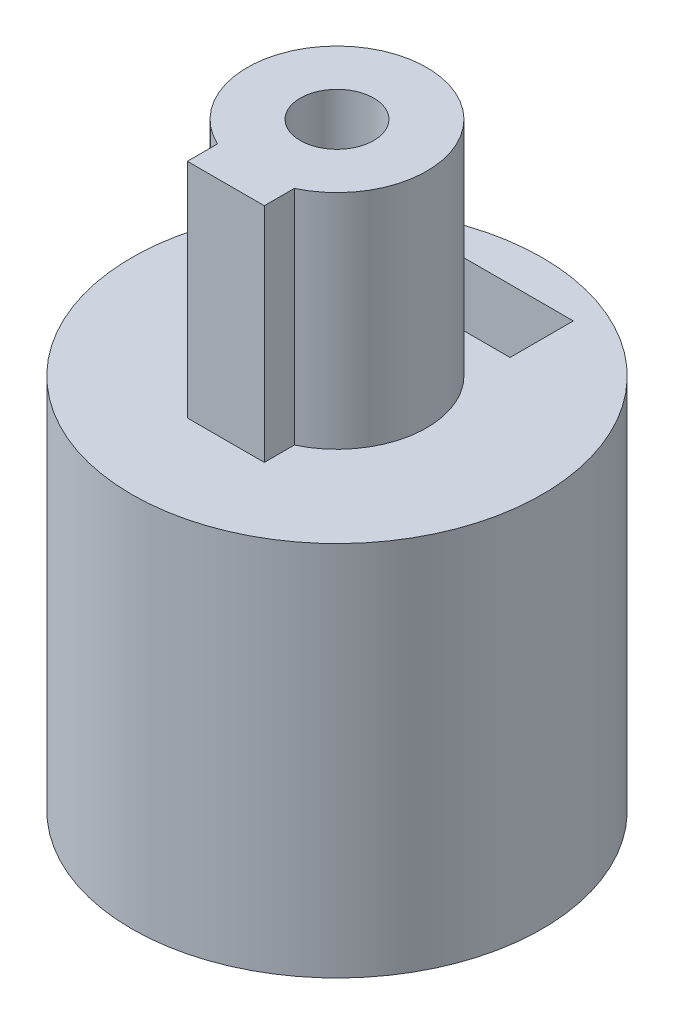
SolidWorks part; units mm, degrees
ref_plane "Front Plane" through (0, 0, 0) normal (0, 0, 1) x (1, 0, 0)
ref_plane "Top Plane" through (0, 0, 0) normal (0, 1, 0) x (1, 0, 0)
ref_plane "Right Plane" through (0, 0, 0) normal (1, 0, 0) x (0, 0, -1)
sketch "Sketch1" plane through (0, 0, 0) normal (0, 1, 0) x (1, 0, 0)
  circle A0 centre (0, 0) radius 1.965 construction
  circle A1 centre (0, 0) radius 6
  dimension "D1" = 3.93
  dimension "D2" = 12
extrude "Boss-Extrude1" add sketch "Sketch1" along normal blind 10
sketch "Sketch2" plane through (0, 0, 0) normal (0, 0, 1) x (1, 0, 0)
  line L0 (0, 10) -> (0, 0) construction
  line L1 (6, 10) -> (-6, 10) construction
  circle A0 centre (0, 7) radius 1.025
  dimension "D1" = 2.05
  dimension "D2" = 3
extrude "Cut-Extrude1" cut sketch "Sketch2" against normal through all
sketch "Sketch4" plane through (0, 0, 0) normal (0, 1, 0) x (1, 0, 0)
  circle A0 centre (0, 0) radius 2.1
  dimension "D1" = 4.2
extrude "Cut-Extrude4" cut sketch "Sketch4" along normal through all
sketch "Sketch5" plane through (0, 10, 0) normal (0, 1, 0) x (1, 0, 0)
  line L0 (-6, 0) -> (6, 0) construction
  line L2 (-0.475, -3.5346) -> (0.475, -3.5346)
  line L3 (-0.475, -3.5346) -> (-0.475, 3.5346)
  line L4 (-0.475, 3.5346) -> (0.475, 3.5346)
  line L5 (0.475, -3.5346) -> (0.475, 3.5346)
  line L6 (0, 3.5346) -> (0, -3.5346) construction
  line L7 (-0.475, 0) -> (0.475, 0) construction
  circle A0 centre (0, 0) radius 6 construction
  point P5 (0, 0)
  dimension "D1" = 0.95
extrude "Boss-Extrude2" add sketch "Sketch5" against normal blind 1.2
sketch "Sketch7" plane through (0, 10, 0) normal (0, 1, 0) x (1, 0, 0)
  circle A0 centre (0, 0) radius 6
  circle A1 centre (0, 0) radius 6 construction
extrude "Boss-Extrude3" add sketch "Sketch7" along normal blind 1
sketch "Sketch8" plane through (0, 11, 0) normal (0, 1, 0) x (1, 0, 0)
  line L0 (0, 0) -> (0, -6) construction
  line L2 (-1.125, -2) -> (1.125, -2)
  line L3 (-1.125, -2) -> (-1.125, -3.25)
  line L4 (-1.125, -3.25) -> (1.125, -3.25)
  line L5 (1.125, -2) -> (1.125, -3.25)
  line L6 (0, -3.25) -> (0, -2) construction
  line L7 (-1.125, -2.625) -> (1.125, -2.625) construction
  circle A0 centre (0, 0) radius 2.625
  circle A1 centre (0, 0) radius 6 construction
  point P3 (0, -2.625)
  dimension "D1" = 5.25
  dimension "D2" = 3.25
  dimension "D3" = 2.25
extrude "Boss-Extrude4" add sketch "Sketch8" along normal blind 6.5 contours A0 L3 L4 L5
sketch "Sketch9" plane through (0, 17.5, 0) normal (0, 1, 0) x (1, 0, 0)
  circle A0 centre (0, 0) radius 1.075
  dimension "D1" = 2.15
extrude "Cut-Extrude5" cut sketch "Sketch9" against normal blind 6
sketch "Sketch3" plane through (0, 0, 0) normal (0, 0, 1) x (1, 0, 0)
  line L1 (0, 4.6213) -> (2.06, 5.8107)
  line L2 (2.06, 5.8107) -> (2.06, 8.1893)
  line L3 (2.06, 8.1893) -> (0, 9.3787) construction
  line L4 (0, 9.3787) -> (-2.06, 8.1893) construction
  line L5 (-2.06, 8.1893) -> (-2.06, 5.8107)
  line L6 (-2.06, 5.8107) -> (0, 4.6213)
  line L10 (-2.06, 8.1893) -> (2.06, 8.1893) construction
  line L11 (-2.06, 8.1893) -> (-2.06, 11.3631)
  line L12 (2.06, 8.1893) -> (2.06, 11.3631)
  line L13 (-2.06, 11.3631) -> (2.06, 11.3631)
  circle A0 centre (0, 7) radius 2.06 construction
  dimension "D1" = 4.12
extrude "Cut-Extrude2" cut sketch "Sketch3" against normal blind 1.85 from offset 3
